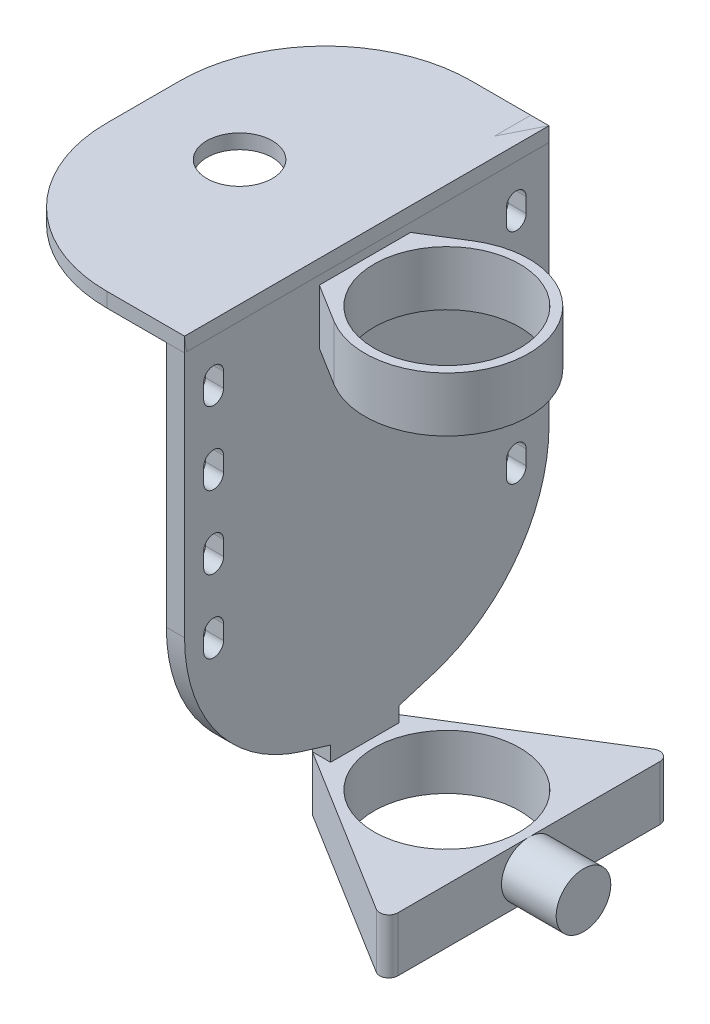
SolidWorks part; units mm, degrees
ref_plane "Front Plane" through (0, 0, 0) normal (0, 0, 1) x (1, 0, 0)
ref_plane "Top Plane" through (0, 0, 0) normal (0, 1, 0) x (1, 0, 0)
ref_plane "Right Plane" through (0, 0, 0) normal (1, 0, 0) x (0, 0, -1)
sketch "Sketch1" plane through (0, 0, 0) normal (0, 1, 0) x (1, 0, 0)
  circle A0 centre (0, 0) radius 4.5
  circle A1 centre (0, 0) radius 4
  dimension "D1" = 9
  dimension "D2" = 8
extrude "Boss-Extrude1" add sketch "Sketch1" along normal mid plane 3
ref_plane "Plane1" through (7.5, 0, 0) normal (1, 0, 0) x (0, 0, -1)
sketch "Sketch4" plane through (7.5, 0, 0) normal (1, 0, 0) x (0, 0, -1)
  circle A0 centre (0, 0) radius 1.5
  dimension "D1" = 3
extrude "Boss-Extrude2" add sketch "Sketch4" against normal up to surface (3.2574 mm away) contours A0
ref_plane "Plane2" through (-4.5, 0, 0) normal (1, 0, 0) x (0, 0, -1)
sketch "Sketch6" plane through (-4.5, 0, 0) normal (1, 0, 0) x (0, 0, -1)
  line L0 (1.8844, -1.5) -> (1.8844, 2.3223)
  line L1 (1.8844, 2.3223) -> (10.1057, 4.8358)
  line L2 (10.1057, 4.8358) -> (10.1057, 25.7738)
  line L3 (10.1057, 25.7738) -> (-9.9029, 25.7738)
  line L4 (-9.9029, 25.7738) -> (-9.9029, 4.7738)
  line L5 (-9.9029, 4.7738) -> (-1.8844, 2.3223)
  line L6 (-1.8844, 2.3223) -> (-1.8844, -1.5)
  line L7 (-1.8844, -1.5) -> (1.8844, -1.5)
  line L8 (0, -9.5117) -> (0, 24.4963) construction
  line L9 (-4.5, -1.5) -> (4.5, -1.5) construction
  dimension "D1" = 107
  dimension "D2" = 21
extrude "Boss-Extrude3" add sketch "Sketch6" against normal blind 1
fillet "Fillet1" radius 9 2 edges at (-5, 4.7738, 9.9029) (-5, 4.8358, -10.1057)
sketch "Sketch7" plane through (-5.5, 0, 0) normal (-1, 0, 0) x (0, 0, 1)
  line L0 (0, 0) -> (0, 27.5191) construction
  line L1 (-8.3067, 23.0308) -> (-8.3067, 22.2308) construction
  line L2 (-7.761, 23.0308) -> (-7.761, 22.2308)
  line L3 (-8.8523, 23.0308) -> (-8.8523, 22.2308)
  arc A0 (-7.761, 23.0308) -> (-8.8523, 23.0308) centre (-8.3067, 23.0308) ccw
  arc A1 (-8.8523, 22.2308) -> (-7.761, 22.2308) centre (-8.3067, 22.2308) ccw
  point P6 (-8.3067, 22.6308)
  dimension "D1" = 0.8
extrude "Cut-Extrude1" cut sketch "Sketch7" against normal blind 1
mirror "Mirror1" about plane through (0, 0, 0) normal (0, 0, 1) of "Cut-Extrude1"
pattern_linear "LPattern1" count 4 spacing 4 along (0, -1, 0) of "Mirror1", "Cut-Extrude1"
sketch "Sketch8" plane through (0, 0, -10.1057) normal (0, 0, -1) x (-1, 0, 0)
  line L0 (4.5, 25.7738) -> (16.767, 25.7738)
  line L1 (4.5, 11.0048) -> (4.5, -11.0048) construction
  line L2 (16.767, 25.7738) -> (16.767, 24.9738)
  line L3 (16.767, 24.9738) -> (4.5, 24.9738)
  line L4 (4.5, 24.9738) -> (4.5, 25.7738)
  line L5 (5.5, 25.7738) -> (4.5, 25.7738) construction
  dimension "D1" = 0.8
extrude "Boss-Extrude4" add sketch "Sketch8" against normal up to surface (20.0087 mm away) up to face at (-5, 18.6036, 9.9029)
fillet "Fillet3" radius 8 2 edges at (-16.767, 25.3738, 9.9029) (-16.767, 25.3738, -10.1057)
sketch "Sketch9" plane through (0, -1.5, 0) normal (0, -1, 0) x (1, 0, 0)
  line L0 (4.5, 8.0855) -> (4.5, -8.0855)
  line L1 (-5.5, 1.8844) -> (4.5, 8.0855)
  line L2 (4.5, -8.0855) -> (-5.5, -1.8844)
  line L3 (-8.8191, 0) -> (9.437, 0) construction
  line L6 (-5.5, 1.8844) -> (-4.5, 1.8844) construction
  line L8 (-5.5, -1.8844) -> (-5.5, 1.8844)
  circle A2 centre (0, 0) radius 4 construction
  circle A4 centre (0, 0) radius 4.5 construction
  circle A5 centre (0, 0) radius 4
extrude "Boss-Extrude5" add sketch "Sketch9" against normal up to surface (3 mm away) up to face at (0, 1.5, 4.5)
fillet "Fillet5" radius 0.5 2 edges at (4.5, 0, -8.0855) (4.5, 0, 8.0855)
sketch "Sketch10" plane through (0, 24.9738, 0) normal (0, -1, 0) x (1, 0, 0)
  circle A0 centre (-11.383, 0) radius 1.7983
ref_plane "Plane3" through (0, 21.5, 0) normal (0, 1, 0) x (1, 0, 0)
sketch "Sketch11" plane through (0, 21.5, 0) normal (0, 1, 0) x (1, 0, 0)
  circle A0 centre (0, 0) radius 4
  circle A1 centre (0, 0) radius 4.5
extrude "Boss-Extrude6" add sketch "Sketch11" along normal blind 3
sketch "Sketch13" plane through (0, 24.5, 0) normal (0, 1, 0) x (1, 0, 0)
  line L0 (-5.5, 1.8844) -> (3.7365, 7.612) construction
  line L1 (3.7365, -7.612) -> (-5.5, -1.8844) construction
  line L2 (-5.5, 1.8844) -> (-2.3715, 3.8244)
  line L3 (-2.3715, -3.8244) -> (-5.5, -1.8844)
  line L4 (-5.5, -1.8844) -> (-5.5, 1.8844)
  circle A0 centre (0, 0) radius 4.5 construction
  arc A1 (-2.3715, 3.8244) -> (-2.3715, -3.8244) centre (0, 0) ccw
extrude "Boss-Extrude7" add sketch "Sketch13" against normal up to surface (3 mm away) up to face at (0, 21.5, 4.5)
extrude "Cut-Extrude3" cut sketch "Sketch10" against normal blind 1 contours A0
